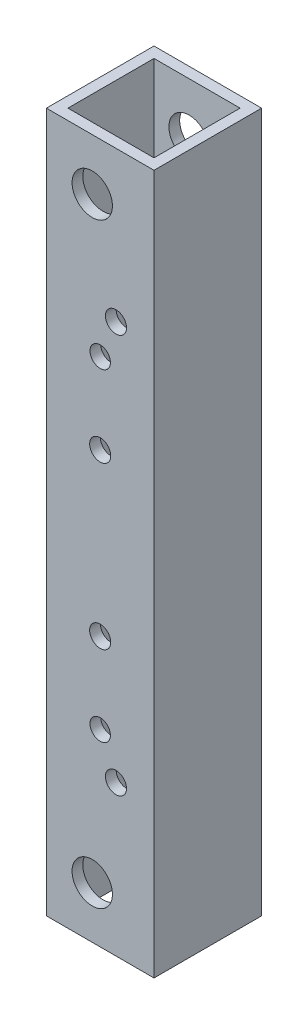
SolidWorks part; units mm, degrees
material "6061-T6 (SS)"
ref_plane "Front Plane" through (0, 0, 0) normal (0, 0, 1) x (1, 0, 0)
ref_plane "Top Plane" through (0, 0, 0) normal (0, 1, 0) x (1, 0, 0)
ref_plane "Right Plane" through (0, 0, 0) normal (1, 0, 0) x (0, 0, -1)
sketch "Sketch1" plane through (0, 0, 0) normal (0, 0, 1) x (1, 0, 0)
  line L0 (0, 0) -> (0, 165.1)
  line L1 (0, 165.1) -> (25.4, 165.1)
  line L2 (25.4, 165.1) -> (25.4, 0)
  line L3 (25.4, 0) -> (0, 0)
  dimension "D1" = 165.1
  dimension "D2" = 25.4
extrude "Boss-Extrude1" add sketch "Sketch1" along normal blind 25.4
sketch "Sketch2" plane through (0, 165.1, 0) normal (0, 1, 0) x (1, 0, 0)
  line L0 (2.54, -2.54) -> (2.54, -22.86)
  line L1 (2.54, -22.86) -> (22.86, -22.86)
  line L2 (22.86, -22.86) -> (22.86, -2.54)
  line L3 (22.86, -2.54) -> (2.54, -2.54)
  line L4 (25.4, 0) -> (0, 0) construction
  line L5 (25.4, -25.4) -> (25.4, 0) construction
  line L6 (25.4, -25.4) -> (0, -25.4) construction
  line L7 (0, -25.4) -> (0, 0) construction
  dimension "D1" = 2.54
  dimension "D2" = 2.54
  dimension "D3" = 2.54
  dimension "D4" = 2.54
extrude "Cut-Extrude1" cut sketch "Sketch2" against normal through all contours L2 L3 L0 L1
sketch "Sketch4" plane through (0, 0, 25.4) normal (0, 0, 1) x (1, 0, 0)
  circle A0 centre (10.8204, 152.91) radius 4.7625
  circle A1 centre (10.8204, 152.91) radius 4.7625 construction
extrude "Cut-Extrude2" cut sketch "Sketch4" against normal through all
ref_plane "Plane1" through (0, 82.55, 0) normal (0, 1, 0) x (1, 0, 0)
mirror "Mirror1" about plane through (0, 82.55, 0) normal (0, 1, 0) of "Cut-Extrude2"
sketch "Sketch5" plane through (0, 0, 25.4) normal (0, 0, 1) x (1, 0, 0)
  circle A1 centre (12.7, 82.55) radius 2.413 construction
  circle A2 centre (12.7, 82.55) radius 2.413
extrude "Cut-Extrude3" [suppressed] cut sketch "Sketch5" against normal through all
sketch "Sketch8" plane through (0, 0, 25.4) normal (0, 0, 1) x (1, 0, 0)
  circle A0 centre (12.7, 63.5) radius 2.4892 construction
  circle A1 centre (12.7, 44.45) radius 2.413 construction
  circle A2 centre (16.4197, 35.4697) radius 2.4892 construction
  circle A3 centre (12.7, 101.6) radius 2.4892 construction
  circle A4 centre (12.7, 120.65) radius 2.413 construction
  circle A5 centre (16.4197, 129.6303) radius 2.4892 construction
  circle A6 centre (12.7, 63.5) radius 2.4892
  circle A7 centre (12.7, 44.45) radius 2.413
  circle A8 centre (16.4197, 35.4697) radius 2.4892
  circle A9 centre (12.7, 101.6) radius 2.4892
  circle A10 centre (12.7, 120.65) radius 2.413
  circle A11 centre (16.4197, 129.6303) radius 2.4892
extrude "Cut-Extrude4" cut sketch "Sketch8" against normal through all
